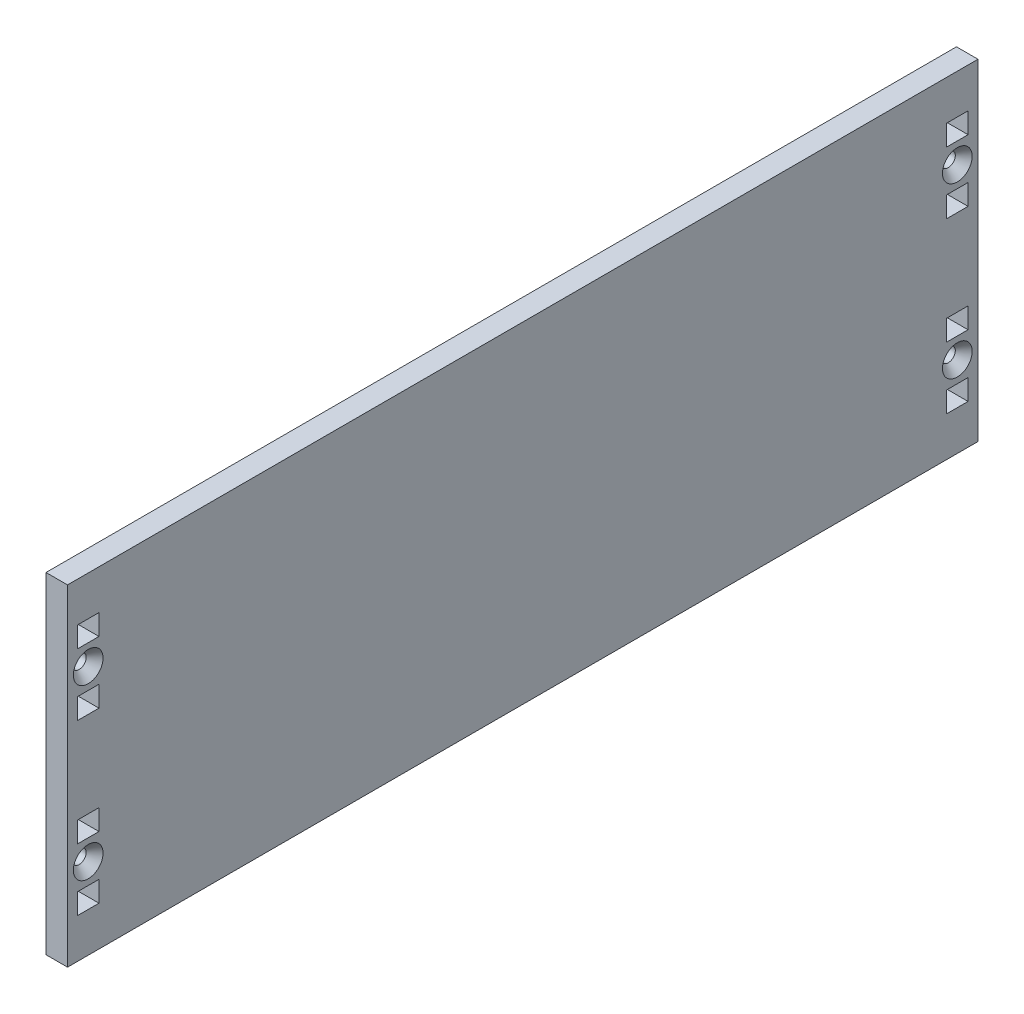
SolidWorks part; units mm, degrees
material "Acrylic (Blue)"
ref_plane "Front Plane" through (0, 0, 0) normal (0, 0, 1) x (1, 0, 0)
ref_plane "Top Plane" through (0, 0, 0) normal (0, 1, 0) x (1, 0, 0)
ref_plane "Right Plane" through (0, 0, 0) normal (1, 0, 0) x (0, 0, -1)
sketch "Sketch1" plane through (0, 0, 0) normal (1, 0, 0) x (0, 0, -1)
  line L0 (133.35, -24.8793) -> (133.35, -76.7207) construction
  line L1 (-139.7, 0) -> (139.7, 0)
  line L2 (-139.7, 0) -> (-139.7, -101.6)
  line L3 (-139.7, -101.6) -> (139.7, -101.6)
  line L4 (139.7, 0) -> (139.7, -101.6)
  line L5 (-133.35, -24.8793) -> (-133.35, -76.7207) construction
  line L6 (0, 0) -> (0, -101.6) construction
  line L7 (-133.35, -50.8) -> (0, -50.8) construction
  line L8 (0, -50.8) -> (133.35, -50.8) construction
  line B0 (-130.048, -31.2293) -> (-130.048, -37.5793)
  line B1 (-130.048, -37.5793) -> (-136.652, -37.5793)
  line B2 (-136.652, -37.5793) -> (-136.652, -31.2293)
  line B3 (-136.652, -31.2293) -> (-130.048, -31.2293)
  line B4 (-130.048, -12.1793) -> (-130.048, -18.5293)
  line B5 (-130.048, -18.5293) -> (-136.652, -18.5293)
  line B6 (-136.652, -18.5293) -> (-136.652, -12.1793)
  line B7 (-136.652, -12.1793) -> (-130.048, -12.1793)
  circle B8 centre (-133.35, -24.8793) radius 2.1526
  line B9 (-130.048, -83.0707) -> (-130.048, -89.4207)
  line B10 (-130.048, -89.4207) -> (-136.652, -89.4207)
  line B11 (-136.652, -89.4207) -> (-136.652, -83.0707)
  line B12 (-136.652, -83.0707) -> (-130.048, -83.0707)
  line B13 (-130.048, -64.0207) -> (-130.048, -70.3707)
  line B14 (-130.048, -70.3707) -> (-136.652, -70.3707)
  line B15 (-136.652, -70.3707) -> (-136.652, -64.0207)
  line B16 (-136.652, -64.0207) -> (-130.048, -64.0207)
  circle B17 centre (-133.35, -76.7207) radius 2.1526
  line B18 (130.048, -18.5293) -> (130.048, -12.1793)
  line B19 (130.048, -12.1793) -> (136.652, -12.1793)
  line B20 (136.652, -12.1793) -> (136.652, -18.5293)
  line B21 (136.652, -18.5293) -> (130.048, -18.5293)
  line B22 (130.048, -37.5793) -> (130.048, -31.2293)
  line B23 (130.048, -31.2293) -> (136.652, -31.2293)
  line B24 (136.652, -31.2293) -> (136.652, -37.5793)
  line B25 (136.652, -37.5793) -> (130.048, -37.5793)
  circle B26 centre (133.35, -24.8793) radius 2.1526
  line B27 (130.048, -70.3707) -> (130.048, -64.0207)
  line B28 (130.048, -64.0207) -> (136.652, -64.0207)
  line B29 (136.652, -64.0207) -> (136.652, -70.3707)
  line B30 (136.652, -70.3707) -> (130.048, -70.3707)
  line B31 (130.048, -89.4207) -> (130.048, -83.0707)
  line B32 (130.048, -83.0707) -> (136.652, -83.0707)
  line B33 (136.652, -83.0707) -> (136.652, -89.4207)
  line B34 (136.652, -89.4207) -> (130.048, -89.4207)
  circle B35 centre (133.35, -76.7207) radius 2.1526
  dimension "D1" = 6.35
  dimension "D2" = 101.6
  dimension "D3" = 266.7
  dimension "D4" = 51.8414
sketch_block_instance "BOLT_HOLE-1"
sketch_block "BOLT_HOLE" parameters "D1"=4.3053, "D2"=6.35, "D3"=6.35, "D4"=6.604
sketch_block_instance "BOLT_HOLE-2"
sketch_block_instance "BOLT_HOLE-3"
sketch_block_instance "BOLT_HOLE-4"
extrude "Boss-Extrude1" add sketch "Sketch1" along normal blind 6.604
hole_wizard "CSK for #8 Flat Head Socket Cap Screw1" positions "Sketch3" profile "Sketch2" countersink size "#8" standard "ANSI Inch" end condition through all
sketch "Sketch3" plane through (6.604, 0, 0) normal (1, 0, 0) x (0, 0, -1)
  point P0 (-133.35, -24.8793)
  point P3 (-133.35, -76.7207)
  point P6 (133.35, -24.8793)
  point P9 (133.35, -76.7207)
sketch "Sketch2" plane through (6.604, -24.8793, 133.35) normal (0, 1, 0) x (0, 0, -1)
  line L0 (0, 0) -> (0, 6.604)
  line L1 (0, 6.604) -> (2.1526, 6.604)
  line L2 (2.1526, 6.604) -> (2.1526, 2.7685)
  line L3 (2.1526, 2.7685) -> (4.5593, 0)
  line L5 (4.5593, 0) -> (0, 0)
  line L6 (-2.1526, 2.7685) -> (-4.5593, 0) construction
  line L11 (0, -6.35) -> (0, 107.95) construction
  dimension "Thru Hole Dia." = 4.3053
  dimension "Thru Hole Depth" = 6.604
  dimension "Near C'Sink Dia." = 9.1186
  dimension "Near C'Sink Angle" = 82
other "Move Face1" [suppressed] parameters "D1"=0.0508
